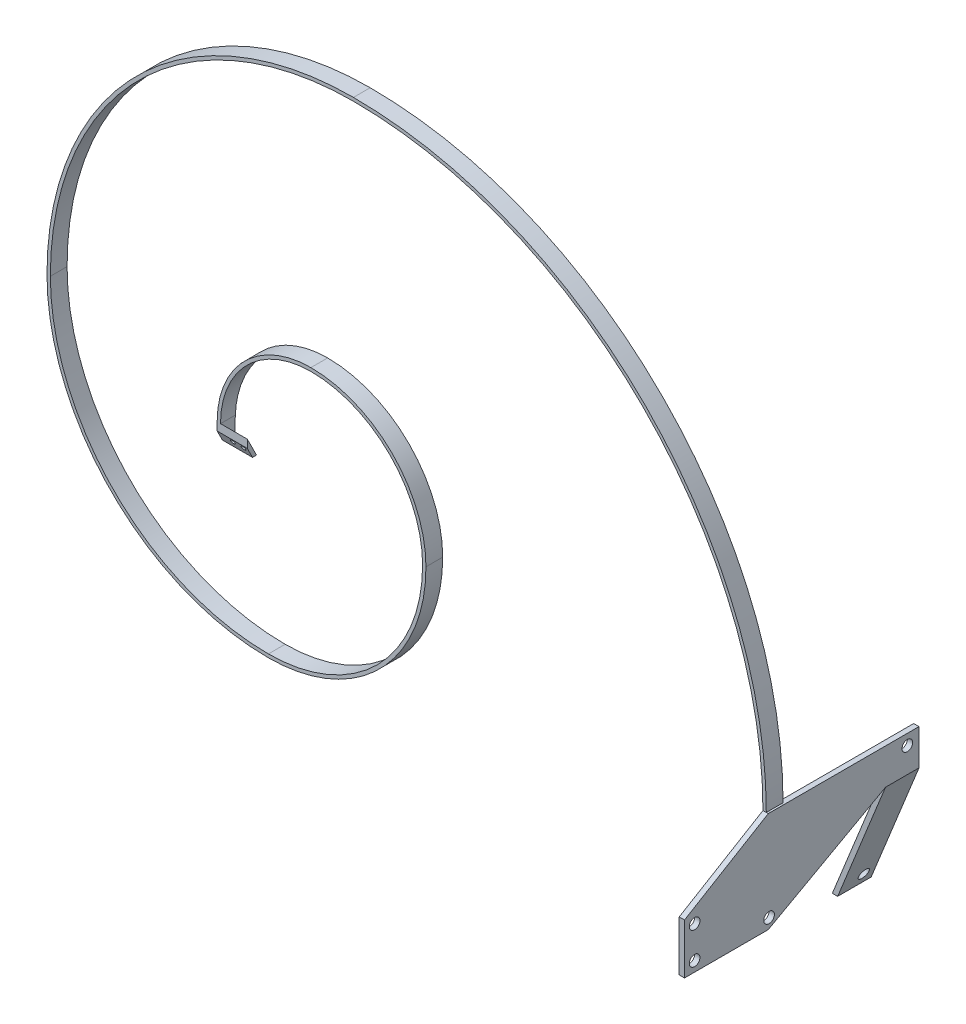
SolidWorks part; units mm, degrees
ref_plane "Front" through (0, 0, 0) normal (0, 0, 1) x (1, 0, 0)
ref_plane "Top" through (0, 0, 0) normal (0, 1, 0) x (1, 0, 0)
ref_plane "Right" through (0, 0, 0) normal (1, 0, 0) x (0, 0, -1)
sketch "Sketch2" plane through (0, 0, 0) normal (0, 0, 1) x (1, 0, 0)
  line L0 (-27.9875, 0) -> (-26.9875, 0)
  line L1 (134.9375, -19.05) -> (135.9375, -19.05)
  arc A0 (-27.9875, 0) -> (0, 27.9875) centre (0, 0) cw
  arc A1 (0, 27.9875) -> (34.3375, -6.35) centre (0, -6.35) cw
  arc A2 (34.3375, -6.35) -> (-12.7, -53.3875) centre (-12.7, -6.35) cw
  arc A3 (-12.7, -53.3875) -> (-78.7875, 12.7) centre (-12.7, 12.7) cw
  arc A4 (-78.7875, 12.7) -> (12.7, 104.1875) centre (12.7, 12.7) cw
  arc A5 (12.7, 104.1875) -> (135.9375, -19.05) centre (12.7, -19.05) cw
  arc A6 (-26.9875, 0) -> (0, 26.9875) centre (0, 0) cw
  arc A7 (0, 26.9875) -> (33.3375, -6.35) centre (0, -6.35) cw
  arc A8 (33.3375, -6.35) -> (-12.7, -52.3875) centre (-12.7, -6.35) cw
  arc A9 (-12.7, -52.3875) -> (-77.7875, 12.7) centre (-12.7, 12.7) cw
  arc A10 (-77.7875, 12.7) -> (12.7, 103.1875) centre (12.7, 12.7) cw
  arc A11 (12.7, 103.1875) -> (134.9375, -19.05) centre (12.7, -19.05) cw
extrude "Extrude2" add sketch "Sketch2" along normal blind 5
sketch "Sketch3" plane through (0, 0, 0) normal (0, -1, 0) x (1, 0, 0)
  line L0 (-78.7875, 0) -> (-12.7, 0) construction
  line L1 (-27.9875, 5) -> (-26.9875, 5)
  line L2 (-27.9875, 5) -> (-27.9875, 0)
  line L3 (-27.9875, 0) -> (-26.9875, 0)
  line L4 (-26.9875, 5) -> (-26.9875, 0)
extrude "Extrude3" add sketch "Sketch3" along normal blind 10
sketch "Sketch6" plane through (-26.9875, 0, 0) normal (1, 0, 0) x (0, 0, -1)
  line L0 (-5, -2.4) -> (-1.2, -10)
  line L1 (-5, -10) -> (-5, 0) construction
  line L2 (0, -10) -> (-5, -10) construction
  line L3 (-1.2, -10) -> (-5, -10)
  line L4 (-5, -10) -> (-5, -2.4)
extrude "Cut-Extrude2" cut sketch "Sketch6" against normal blind 5
sketch "Sketch7" plane through (-26.9875, 0, 0) normal (1, 0, 0) x (0, 0, -1)
  line L0 (-5, 0) -> (0, -10)
  line L1 (0, -10) -> (-1.2, -10)
  line L2 (-1.2, -10) -> (-5, -2.4)
  line L3 (-5, -2.4) -> (-5, 0)
extrude "Extrude5" add sketch "Sketch7" along normal blind 8
sketch "Sketch8" plane through (0, -19.05, 0) normal (0, -1, 0) x (1, 0, 0)
  line L1 (134.9375, 5) -> (136.525, 5)
  line L2 (134.9375, 5) -> (134.9375, 0)
  line L3 (134.9375, 0) -> (136.525, 0)
  line L4 (136.525, 5) -> (136.525, 0)
extrude "Extrude6" add sketch "Sketch8" along normal blind 30
sketch "Sketch9" plane through (0, 0, 0) normal (0, 0, -1) x (-1, 0, 0)
  line L1 (-136.525, -49.05) -> (-134.9375, -49.05)
  line L2 (-136.525, -49.05) -> (-136.525, -19.05)
  line L3 (-136.525, -19.05) -> (-134.9375, -19.05)
  line L4 (-134.9375, -49.05) -> (-134.9375, -19.05)
extrude "Extrude7" add sketch "Sketch9" along normal blind 30
sketch "Sketch10" plane through (0, 0, 5) normal (0, 0, 1) x (1, 0, 0)
  line L1 (134.9375, -19.05) -> (136.525, -19.05)
  line L2 (134.9375, -19.05) -> (134.9375, -49.05)
  line L3 (134.9375, -49.05) -> (136.525, -49.05)
  line L4 (136.525, -19.05) -> (136.525, -49.05)
extrude "Extrude8" add sketch "Sketch10" along normal blind 25
sketch "Sketch11" plane through (134.9375, 0, 0) normal (-1, 0, 0) x (0, 0, 1)
  line L0 (5, -19.05) -> (30, -34.05)
  line L1 (30, -19.05) -> (30, -49.05) construction
  line L2 (30, -34.05) -> (30, -19.05)
  line L3 (30, -19.05) -> (5, -19.05)
extrude "Cut-Extrude3" cut sketch "Sketch11" against normal blind 5
sketch "Sketch12" plane through (134.9375, 0, 0) normal (-1, 0, 0) x (0, 0, 1)
  line L0 (5, -49.05) -> (-30, -29.7287)
  line L1 (5, -53.3875) -> (5, 12.7) construction
  line L2 (-30, -29.7287) -> (-30, -49.05)
  line L3 (-30, -49.05) -> (5, -49.05)
extrude "Cut-Extrude4" cut sketch "Sketch12" against normal blind 5
sketch "Sketch14" plane through (-27.9875, 0, 0) normal (-1, 0, 0) x (0, 0, 1)
  line L0 (0, -5.5) -> (0, 14)
  line L1 (0, -10) -> (4.7625, -10)
  line L2 (0, -10) -> (0, -5.5)
  line L3 (0, 12.7) -> (0, -53.3875) construction
  line L4 (4.7625, -10) -> (4.7625, -5.5)
  line L5 (0, 14) -> (0.8, -5.5)
  line L6 (0.8, -5.5) -> (4.7625, -5.5)
extrude "Cut-Extrude6" cut sketch "Sketch14" against normal blind 15
sketch "Sketch15" plane through (0, -2, 4) normal (0, 0.4472, -0.8944) x (-1, 0, 0)
  circle A0 centre (23.8125, -1) radius 0.7
  circle A1 centre (20.6375, -1) radius 0.7
  dimension "D1" = 3.175
extrude "Cut-Extrude7" cut sketch "Sketch15" against normal blind 10
sketch "Sketch17" plane through (0, 0, -30) normal (0, 0, -1) x (-1, 0, 0)
  line L0 (-136.525, -19.05) -> (-136.525, -29.7287)
  line L1 (-136.525, -29.7287) -> (-122.24, -65.09)
  line L2 (-122.24, -65.09) -> (-120.65, -65.09)
  line L3 (-120.65, -65.09) -> (-134.9375, -29.7287)
  line L4 (-134.9375, -29.7287) -> (-134.9375, -19.05)
  line L5 (-134.9375, -19.05) -> (-136.525, -19.05)
extrude "Extrude9" add sketch "Sketch17" along normal blind 10
sketch "Sketch18" plane through (126.3263, -51.0413, 0) normal (-0.9272, 0.3746, 0) x (0, 0, 1)
  circle A0 centre (-36.5125, -11.1125) radius 1.5875
extrude "Cut-Extrude8" cut sketch "Sketch18" against normal blind 3
sketch "Sketch19" plane through (136.525, 0, 0) normal (1, 0, 0) x (0, 0, -1)
  circle A0 centre (-26.9875, -46.0375) radius 1.5875
  circle A1 centre (-26.9875, -36.5125) radius 1.5875
  circle A2 centre (-4.7625, -46.0375) radius 1.5875
  circle A3 centre (36.5125, -22.225) radius 1.5875
extrude "Cut-Extrude9" cut sketch "Sketch19" against normal blind 3
